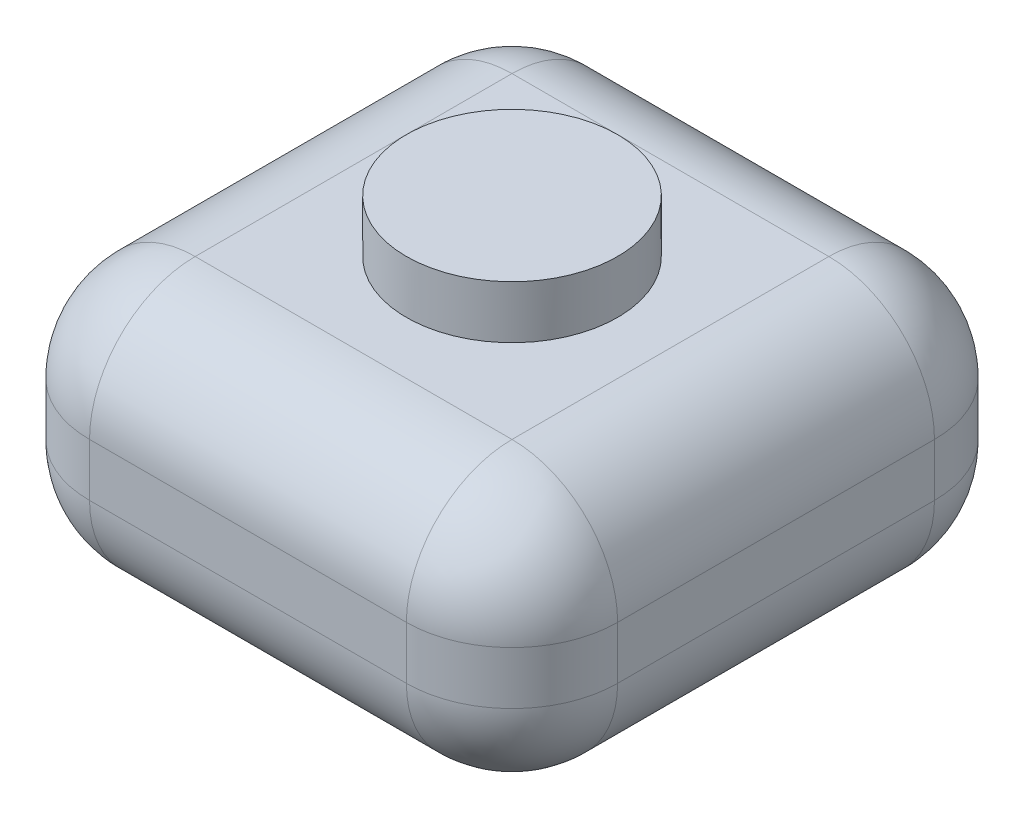
SolidWorks part; units mm, degrees
ref_plane "前视基准面" through (0, 0, 0) normal (0, 0, 1) x (1, 0, 0)
ref_plane "上视基准面" through (0, 0, 0) normal (0, 1, 0) x (1, 0, 0)
ref_plane "右视基准面" through (0, 0, 0) normal (1, 0, 0) x (0, 0, -1)
other "Configuration Table"
sketch "草图1" plane through (0, 0, 0) normal (0, 1, 0) x (1, 0, 0)
  line L1 (-5, -5) -> (5, -5)
  line L2 (-5, -5) -> (-5, 5)
  line L3 (-5, 5) -> (5, 5)
  line L4 (5, -5) -> (5, 5)
  line L5 (-5, -5) -> (5, 5) construction
  line L6 (-5, 5) -> (5, -5) construction
  point P0 (0, 0)
extrude "凸台-拉伸1" add sketch "草图1" along normal blind 5 contours L3 L4 L1 L2
fillet "圆角2" radius 2 12 edges at (-5, 2.5, -5) (-5, 5, 0) (-5, 0, 0) (-5, 2.5, 5) (0, 5, 5) (5, 2.5, 5) (0, 0, 5) (0, 5, -5) (0, 0, -5) (5, 5, 0) (5, 2.5, -5) (5, 0, 0)
sketch "草图2" plane through (0, 5, 0) normal (0, 1, 0) x (1, 0, 0)
  circle A0 centre (0, 0) radius 2
extrude "凸台-拉伸2" add sketch "草图2" along normal blind 1
